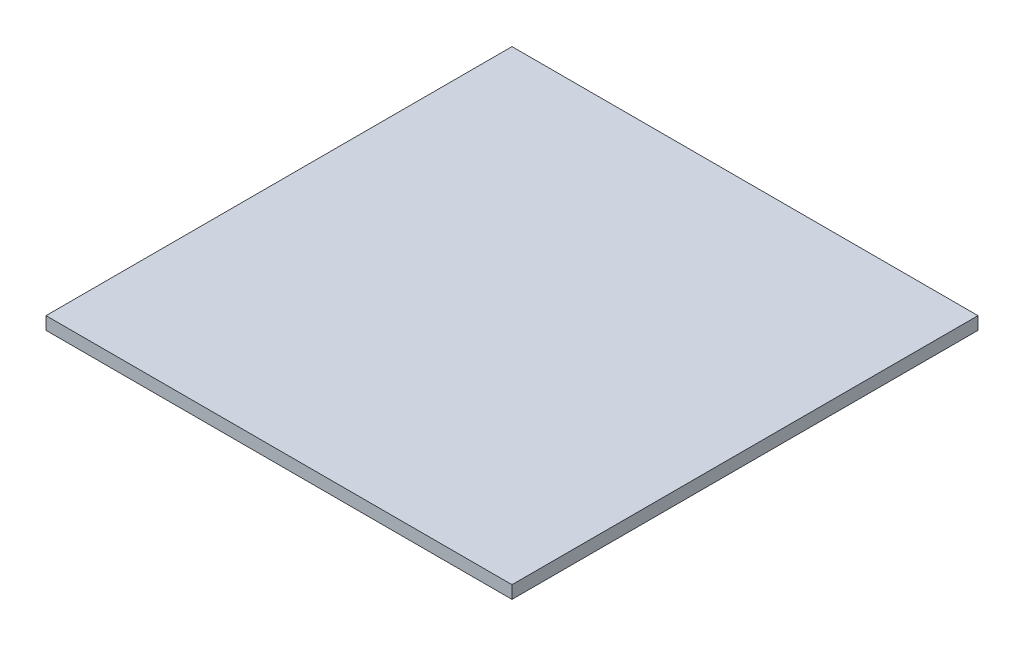
SolidWorks part; units mm, degrees
ref_plane "Front Plane" through (0, 0, 0) normal (0, 0, 1) x (1, 0, 0)
ref_plane "Top Plane" through (0, 0, 0) normal (0, 1, 0) x (1, 0, 0)
ref_plane "Right Plane" through (0, 0, 0) normal (1, 0, 0) x (0, 0, -1)
sketch "Sketch2" plane through (0, 0, 0) normal (0, 1, 0) x (1, 0, 0)
  line L1 (-118.587, 65.1335) -> (-36.037, 65.1335)
  line L2 (-118.587, 65.1335) -> (-118.587, -17.4165)
  line L3 (-118.587, -17.4165) -> (-36.037, -17.4165)
  line L4 (-36.037, 65.1335) -> (-36.037, -17.4165)
  dimension "D1" = 82.55
  dimension "D2" = 82.55
extrude "Boss-Extrude1" add sketch "Sketch2" along normal blind 2.2606
